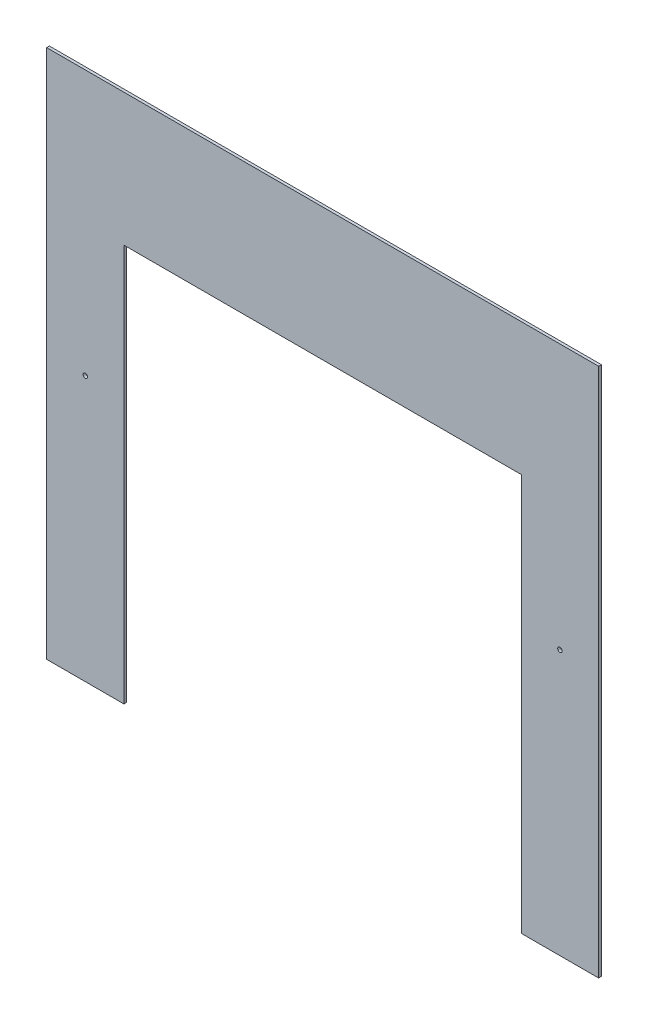
SolidWorks part; units mm, degrees
ref_plane "Front Plane" through (0, 0, 0) normal (0, 0, 1) x (1, 0, 0)
ref_plane "Top Plane" through (0, 0, 0) normal (0, 1, 0) x (1, 0, 0)
ref_plane "Right Plane" through (0, 0, 0) normal (1, 0, 0) x (0, 0, -1)
sketch "Sketch1" plane through (0, 0, 0) normal (0, 0, 1) x (1, 0, 0)
  line L0 (-441.3958, 526.5377) -> (193.6042, 526.5377)
  line L1 (193.6042, 526.5377) -> (193.6042, -83.0623)
  line L2 (193.6042, -83.0623) -> (104.7042, -83.0623)
  line L3 (104.7042, -83.0623) -> (104.7042, 374.1377)
  line L5 (-441.3958, 36.4853) -> (-441.3958, 526.5377)
  line L6 (-441.3958, 36.4853) -> (-441.3958, -83.0623)
  line L7 (-441.3958, -83.0623) -> (-352.4958, -83.0623)
  line L8 (-352.4958, -83.0623) -> (-352.4958, 374.1377)
  line L9 (-352.4958, 374.1377) -> (104.7042, 374.1377)
  point P5 (-441.3958, -23.2885)
  dimension "D1" = 635
  dimension "D2" = 609.6
  dimension "D3" = 609.6
  dimension "D4" = 88.9
  dimension "D5" = 88.9
  dimension "D6" = 152.4
extrude "Boss-Extrude1" add sketch "Sketch1" along normal blind 3.175
sketch "Sketch2" plane through (0, 0, 3.175) normal (0, 0, 1) x (1, 0, 0)
  line L0 (-441.3958, 526.5377) -> (-441.3958, -83.0623) construction
  line L1 (193.6042, -83.0623) -> (193.6042, 526.5377) construction
  line L2 (193.6042, 526.5377) -> (-441.3958, 526.5377) construction
  line L3 (-441.3958, -83.0623) -> (-352.4958, -83.0623) construction
  circle A0 centre (-396.9458, 221.7377) radius 2.5797
  circle A1 centre (149.1542, 221.7377) radius 2.5797
  dimension "D5" = 5.1594
  dimension "D6" = 5.1594
  dimension "D1" = 44.45
  dimension "D2" = 44.45
  dimension "D3" = 304.8
  dimension "D4" = 304.8
extrude "Cut-Extrude1" cut sketch "Sketch2" against normal through all
